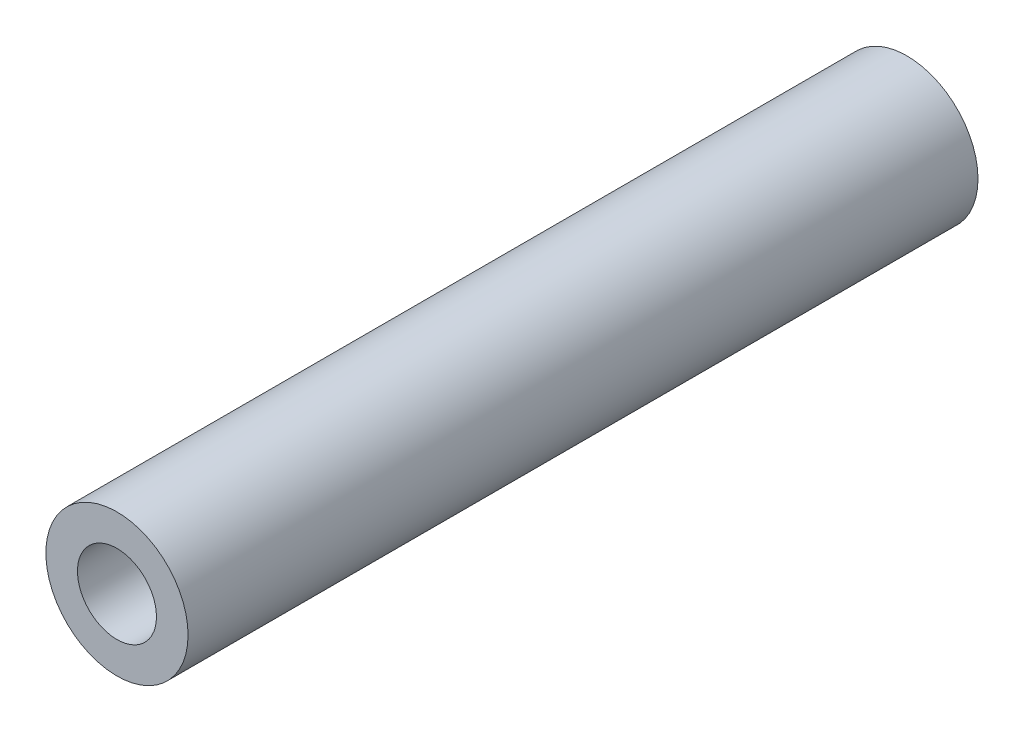
SolidWorks part; units mm, degrees
material "Nylon 101"
ref_plane "Front Plane" through (0, 0, 0) normal (0, 0, 1) x (1, 0, 0)
ref_plane "Top Plane" through (0, 0, 0) normal (0, 1, 0) x (1, 0, 0)
ref_plane "Right Plane" through (0, 0, 0) normal (1, 0, 0) x (0, 0, -1)
sketch "Sketch1" plane through (0, 0, 0) normal (0, 0, 1) x (1, 0, 0)
  circle A0 centre (0, 0) radius 1.5875
  circle A1 centre (0, 0) radius 2.8575
  dimension "D1" = 3.175
  dimension "D2" = 5.715
extrude "Boss-Extrude1" add sketch "Sketch1" along normal blind 31.75
